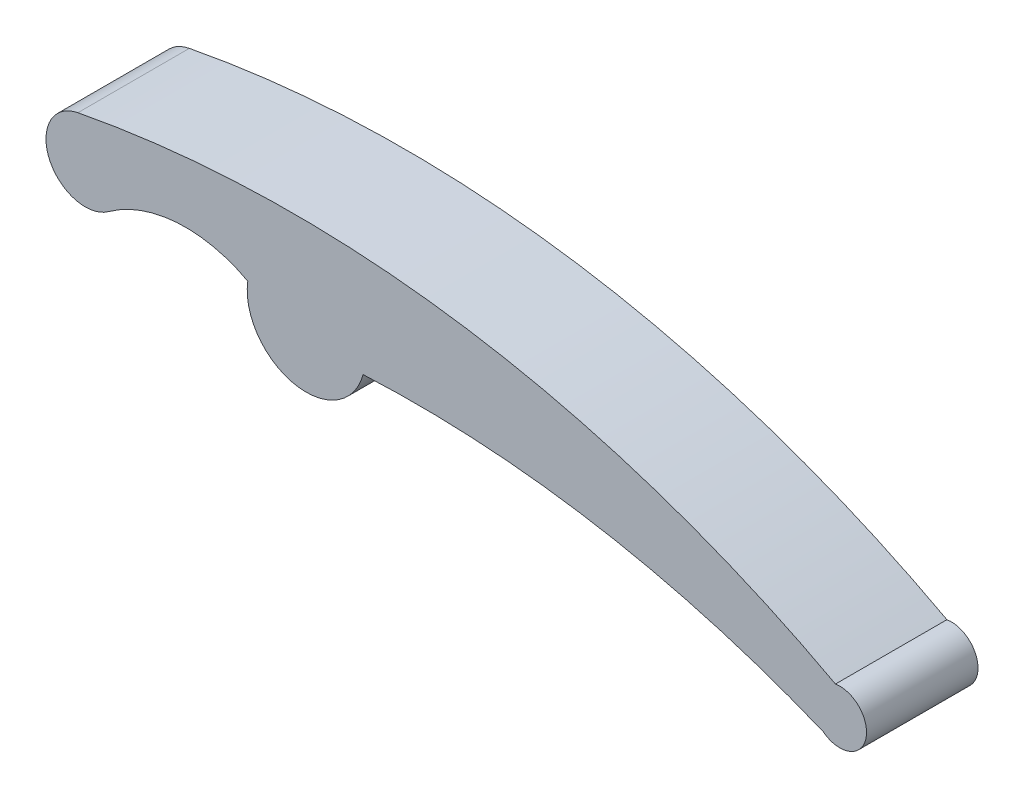
SolidWorks part; units mm, degrees
ref_plane "前视基准面" through (0, 0, 0) normal (0, 0, 1) x (1, 0, 0)
ref_plane "上视基准面" through (0, 0, 0) normal (0, 1, 0) x (1, 0, 0)
ref_plane "右视基准面" through (0, 0, 0) normal (1, 0, 0) x (0, 0, -1)
sketch "草图1" plane through (0, 0, 0) normal (0, 0, 1) x (1, 0, 0)
  arc A0 (-15.7123, 2.1607) -> (15.3229, -4.0934) centre (0, 0) ccw
  arc A1 (15.3229, -4.0934) -> (139.1973, -25.4167) centre (29.5225, -292.0785) cw
  arc A2 (-61.4364, 18.5702) -> (142.4812, -12.6547) centre (-3.3809, -283.7577) cw
  arc A3 (-61.4364, 18.5702) -> (-53.2175, -0.3858) centre (-59.4404, 8.1759) ccw
  arc A4 (142.4812, -12.6547) -> (139.1973, -25.4167) centre (143.6475, -19.7583) cw
  arc A5 (-53.2175, -0.3858) -> (-15.7123, 2.1607) centre (-32.4373, -28.9759) cw
  dimension "D1" = 145
  dimension "D2" = 60
extrude "凸台-拉伸1" add sketch "草图1" along normal blind 30
